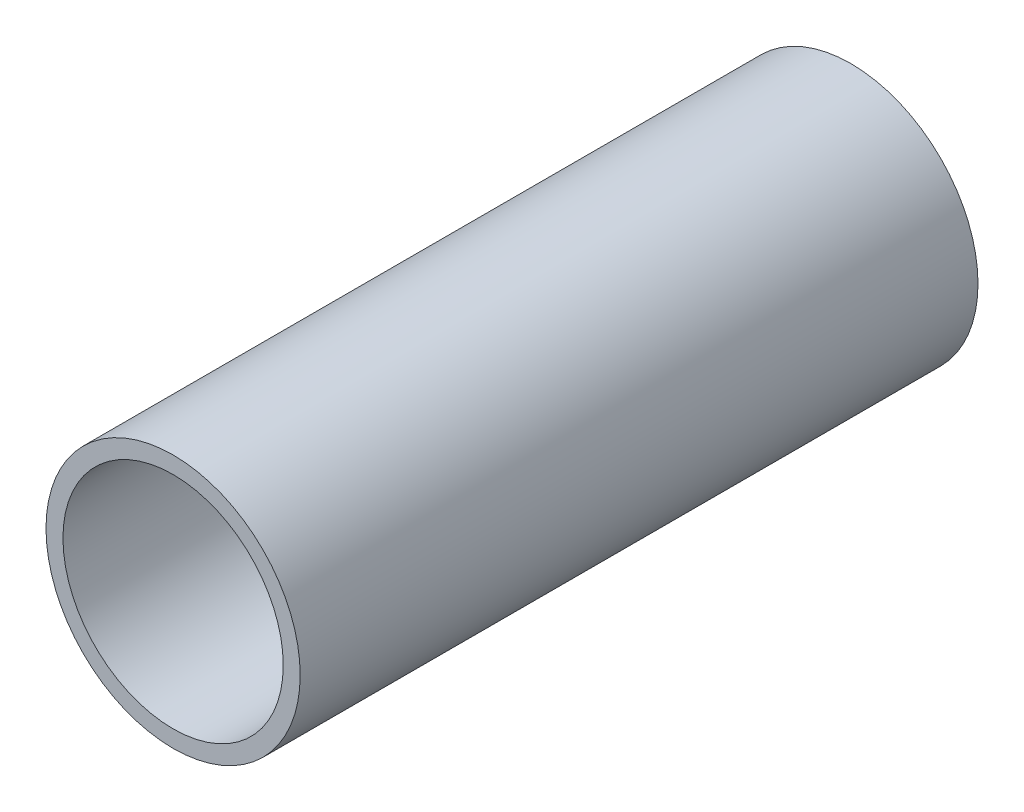
SolidWorks part; units mm, degrees
ref_plane "前视基准面" through (0, 0, 0) normal (0, 0, 1) x (1, 0, 0)
ref_plane "上视基准面" through (0, 0, 0) normal (0, 1, 0) x (1, 0, 0)
ref_plane "右视基准面" through (0, 0, 0) normal (1, 0, 0) x (0, 0, -1)
sketch "草图1" plane through (0, 0, 0) normal (0, 0, 1) x (1, 0, 0)
  circle A0 centre (0, 0) radius 15
  circle A1 centre (0, 0) radius 13
extrude "凸台-拉伸1" add sketch "草图1" against normal blind 80
